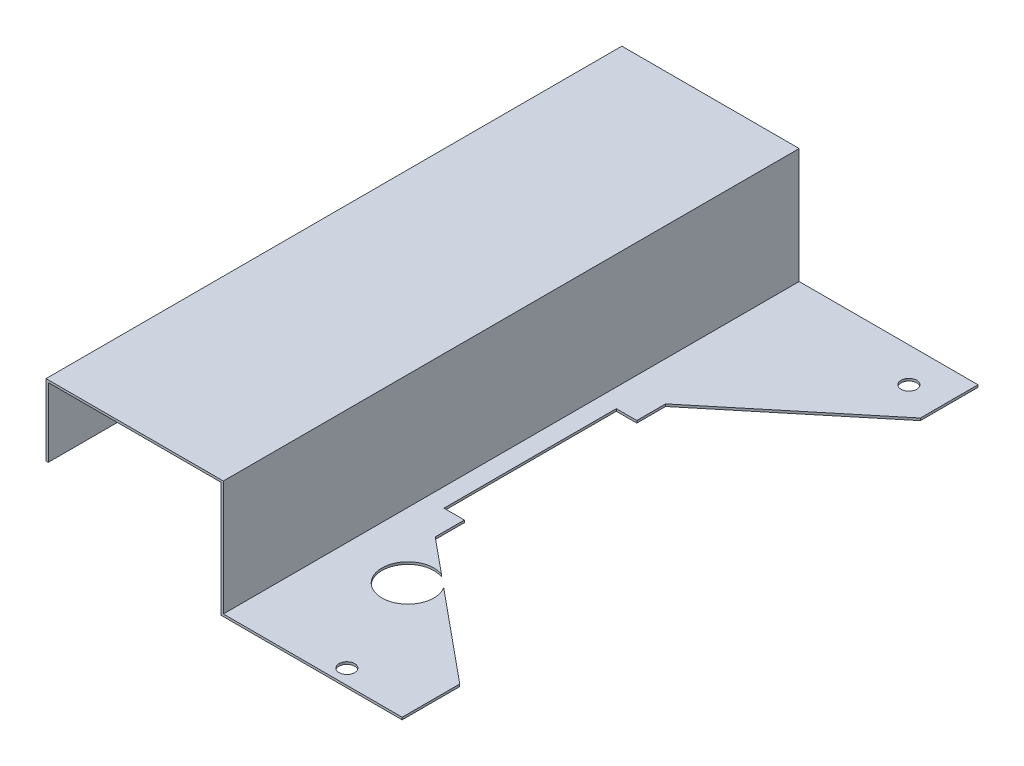
SolidWorks part; units mm, degrees
ref_plane "Front Plane" through (0, 0, 0) normal (0, 0, 1) x (1, 0, 0)
ref_plane "Top Plane" through (0, 0, 0) normal (0, 1, 0) x (1, 0, 0)
ref_plane "Right Plane" through (0, 0, 0) normal (1, 0, 0) x (0, 0, -1)
sketch "Sketch1" plane through (0, 0, 0) normal (0, 0, 1) x (1, 0, 0)
  line L0 (-13.1819, 17.7) -> (-13.1819, 47.7)
  line L1 (-13.1819, 47.7) -> (61.8181, 47.7)
  line L2 (61.8181, 47.7) -> (61.8181, -2.3)
  line L3 (61.8181, -2.3) -> (79.8181, -2.3)
  line L4 (79.8181, -2.3) -> (79.8181, -1.3)
  line L5 (79.8181, -1.3) -> (62.8181, -1.3)
  line L6 (62.8181, -1.3) -> (62.8181, 48.7)
  line L7 (62.8181, 48.7) -> (-14.1819, 48.7)
  line L8 (-14.1819, 48.7) -> (-14.1819, 17.7)
  line L9 (-14.1819, 17.7) -> (-13.1819, 17.7)
  dimension "D1" = 1
  dimension "D2" = 1
  dimension "D3" = 1
  dimension "D4" = 1
  dimension "D5" = 50
  dimension "D6" = 30
  dimension "D7" = 75
  dimension "D8" = 17
extrude "Boss-Extrude1" add sketch "Sketch1" along normal mid plane 250
sketch "Sketch2" plane through (0, -2.3, 0) normal (0, -1, 0) x (1, 0, 0)
  line L0 (79.8181, 125) -> (79.8181, -125) construction
  line L1 (79.8181, -125) -> (140.4464, -125)
  line L5 (79.8181, 125) -> (140.4464, 125)
  line L8 (140.4464, 125) -> (140.4464, 100)
  line L9 (140.4464, 100) -> (79.8181, 50)
  line L11 (140.4464, -125) -> (140.4464, -100)
  line L12 (79.8181, -125) -> (79.8181, -50)
  line L13 (140.4464, -100) -> (79.8181, -50)
  line M4 (79.8181, -125) -> (79.8181, 125)
  dimension "D1" = 75
  dimension "D2" = 25
  dimension "D3" = 75
  dimension "D4" = 25
extrude "Boss-Extrude3" add sketch "Sketch2" against normal up to surface (1 mm away) contours L9 L8 L5 M4 | L11 L13 L1 M4 up to face at (71.3181, -1.3, 0)
hole_wizard "Tap Drill for M8 Tap1" positions "Sketch6" profile "Sketch5" hole size "M8" standard "ISO" end condition through all
sketch "Sketch6" plane through (0, -2.3, 0) normal (0, -1, 0) x (-1, 0, 0)
  line L2 (-61.8181, 125) -> (-140.4464, 125) construction
  line L3 (-140.4464, 125) -> (-140.4464, 100) construction
  point P2 (-125.4464, 110)
  point P14 (-109.9748, -118.5487)
  point P18 (0, 0)
  dimension "D3" = 15
  dimension "D4" = 15
sketch "Sketch5" plane through (125.4464, -2.3, -110) normal (1, 0, 0) x (0, 0, -1)
  line L0 (0, 0) -> (0, 51)
  line L1 (0, 51) -> (3.4, 51)
  line L2 (3.4, 51) -> (3.4, 0)
  line L5 (3.4, 0) -> (0, 0)
  line L11 (0, -6.35) -> (0, 107.95) construction
  dimension "Thru Hole Dia." = 6.8
  dimension "Thru Hole Depth" = 51
sketch "Sketch7" plane through (0, -2.3, 0) normal (0, -1, 0) x (1, 0, 0)
  circle A0 centre (91.2233, 73.2787) radius 11.2881
extrude "Cut-Extrude1" cut sketch "Sketch7" against normal blind 1 contours A0
sketch "Sketch8" plane through (0, -2.3, 0) normal (0, -1, 0) x (1, 0, 0)
  line L1 (70.9189, -37.4979) -> (88.5243, -37.4979)
  line L2 (70.9189, -37.4979) -> (70.9189, 37.343)
  line L3 (70.9189, 37.343) -> (88.5243, 37.343)
  line L4 (88.5243, -37.4979) -> (88.5243, 37.343)
extrude "Cut-Extrude2" cut sketch "Sketch8" against normal blind 1 contours L2 L3 L4 L1
